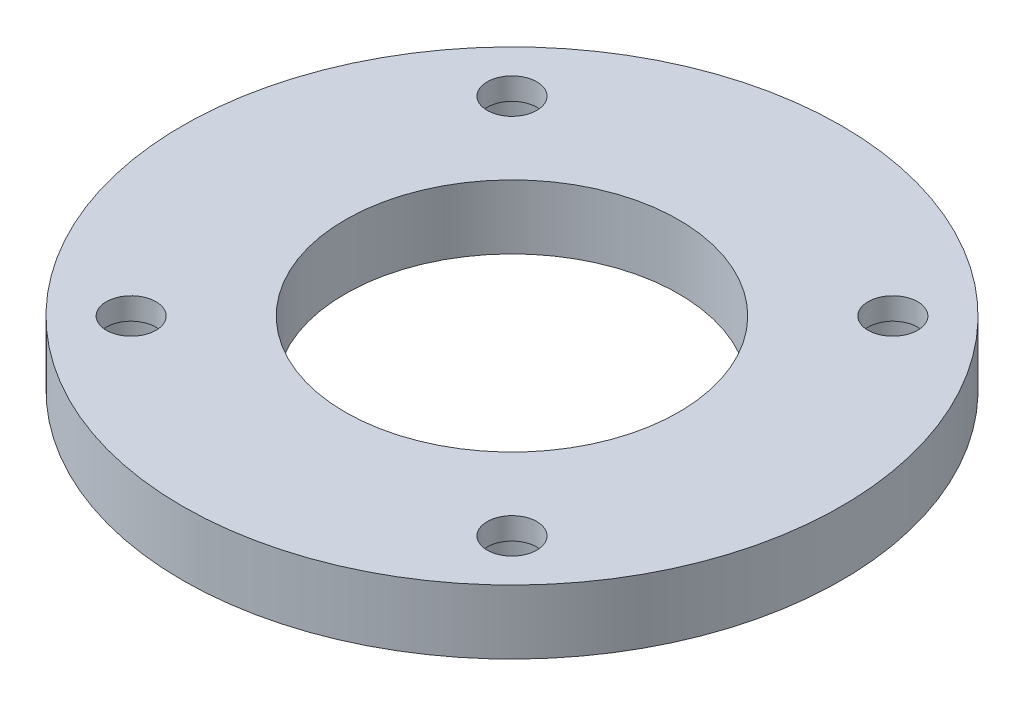
SolidWorks part; units mm, degrees
material "6061-T6 (SS)"
ref_plane "Front" through (0, 0, 0) normal (0, 0, 1) x (1, 0, 0)
ref_plane "Top" through (0, 0, 0) normal (0, 1, 0) x (1, 0, 0)
ref_plane "Right" through (0, 0, 0) normal (1, 0, 0) x (0, 0, -1)
sketch "Sketch1" plane through (0, 0, 0) normal (0, 1, 0) x (1, 0, 0)
  circle A0 centre (0, 0) radius 16.51
  circle A1 centre (0, 0) radius 32.639
  dimension "D1" = 33.02
  dimension "D2" = 65.278
extrude "Extrude1" add sketch "Sketch1" along normal blind 6.35
sketch "hole positions" plane through (0, 0, 0) normal (0, -1, 0) x (1, 0, 0)
  line L0 (-18.8585, 18.8585) -> (18.8585, -18.8585) construction
  line L1 (-18.8585, 18.8585) -> (18.8585, 18.8585)
  line L2 (-18.8585, 18.8585) -> (-18.8585, -18.8585)
  line L3 (-18.8585, -18.8585) -> (18.8585, -18.8585)
  line L4 (18.8585, 18.8585) -> (18.8585, -18.8585)
  point P4 (0, 0)
  dimension "D1" = 53.34
hole_wizard "CBORE for #8 Socket Head Cap Screw1" positions "3DSketch1" profile "Sketch3" counterbore size "#8" standard "Ansi Inch" end condition through all
sketch3d "3DSketch1"
  point P0 (-18.8585, 0, 18.8585)
  point P3 (18.8585, 0, 18.8585)
  point P6 (18.8585, 0, -18.8585)
  point P9 (-18.8585, 0, -18.8585)
sketch "Sketch3" plane through (-18.8585, 0, 18.8585) normal (1, 0, 0) x (0, 0, -1)
  line L0 (0, 0) -> (0, 6.35)
  line L1 (0, 6.35) -> (2.4574, 6.35)
  line L3 (2.4574, 6.35) -> (2.4575, 4.1656)
  line L4 (2.4575, 4.1656) -> (3.9688, 4.1656)
  line L5 (3.9688, 4.1656) -> (3.9687, 0)
  line L7 (3.9687, 0) -> (0, 0)
  line L11 (0, -6.35) -> (0, 107.95) construction
  dimension "Thru Hole Dia." = 4.9149
  dimension "Thru Hole Depth" = 6.35
  dimension "C'Bore Dia." = 7.9375
  dimension "C'Bore Depth" = 4.1656
